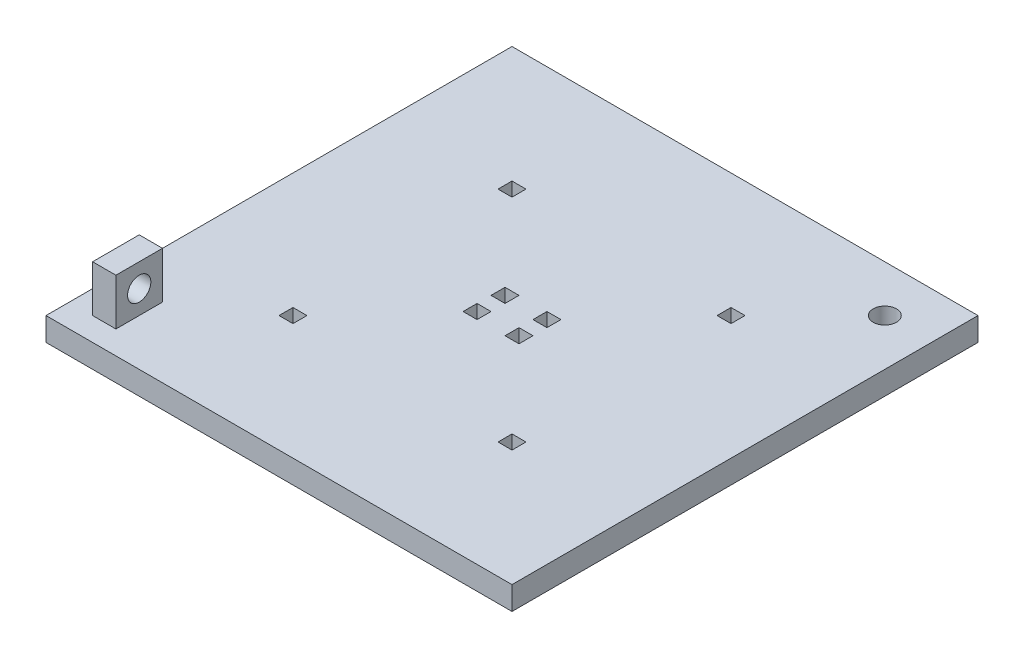
SolidWorks part; units mm, degrees
ref_plane "Front Plane" through (0, 0, 0) normal (0, 0, 1) x (1, 0, 0)
ref_plane "Top Plane" through (0, 0, 0) normal (0, 1, 0) x (1, 0, 0)
ref_plane "Right Plane" through (0, 0, 0) normal (1, 0, 0) x (0, 0, -1)
sketch "Sketch1" plane through (0, 0, 0) normal (0, 1, 0) x (1, 0, 0)
  line L0 (0, 50) -> (0, -50) construction
  line L1 (-50, 50) -> (50, 50)
  line L2 (-50, 50) -> (-50, -50)
  line L3 (-50, -50) -> (50, -50)
  line L4 (50, 50) -> (50, -50)
  line L5 (-25, 25) -> (-22, 25)
  line L6 (-25, 25) -> (-25, 22)
  line L7 (-25, 22) -> (-22, 22)
  line L8 (-22, 25) -> (-22, 22)
  line L9 (-50, 0) -> (50, 0) construction
  line L10 (22, 25) -> (22, 22)
  line L11 (25, 22) -> (22, 22)
  line L12 (25, 25) -> (25, 22)
  line L13 (25, 25) -> (22, 25)
  line L14 (25, -25) -> (22, -25)
  line L15 (25, -25) -> (25, -22)
  line L16 (25, -22) -> (22, -22)
  line L17 (22, -25) -> (22, -22)
  line L18 (-22, -25) -> (-22, -22)
  line L19 (-25, -22) -> (-22, -22)
  line L20 (-25, -25) -> (-25, -22)
  line L21 (-25, -25) -> (-22, -25)
  line L22 (3, 4.5) -> (3, 1.5)
  line L23 (-6, 4.5) -> (-3, 4.5)
  line L24 (-6, 4.5) -> (-6, 1.5)
  line L25 (-6, 1.5) -> (-3, 1.5)
  line L26 (-3, 4.5) -> (-3, 1.5)
  line L27 (6, 1.5) -> (3, 1.5)
  line L28 (6, 4.5) -> (6, 1.5)
  line L29 (6, 4.5) -> (3, 4.5)
  line L30 (6, -4.5) -> (3, -4.5)
  line L31 (6, -4.5) -> (6, -1.5)
  line L32 (6, -1.5) -> (3, -1.5)
  line L33 (-3, -4.5) -> (-3, -1.5)
  line L34 (-6, -1.5) -> (-3, -1.5)
  line L35 (-6, -4.5) -> (-6, -1.5)
  line L36 (-6, -4.5) -> (-3, -4.5)
  line L37 (3, -4.5) -> (3, -1.5)
  circle A0 centre (40, 40) radius 2.5
  point P12 (-50, 0)
  point P17 (0, 0)
  point P19 (-23.5, 25)
  dimension "D10" = 5
  dimension "D11" = 10
  dimension "D12" = 10
  dimension "D1" = 100
  dimension "D2" = 100
  dimension "D3" = 3
  dimension "D4" = 25
  dimension "D5" = 25
  dimension "D6" = 3
  dimension "D7" = 3
  dimension "D8" = 6
  dimension "D9" = 3
extrude "Boss-Extrude1" add sketch "Sketch1" along normal blind 5
sketch "Sketch4" plane through (0, 5, 0) normal (0, 1, 0) x (1, 0, 0)
  line L0 (-50, 50) -> (-50, -50) construction
  line L1 (-45, -35) -> (-40, -35)
  line L2 (-45, -35) -> (-45, -45)
  line L3 (-45, -45) -> (-40, -45)
  line L4 (-40, -35) -> (-40, -45)
  line L5 (-50, -50) -> (50, -50) construction
  dimension "D1" = 10
  dimension "D2" = 5
  dimension "D3" = 5
  dimension "D4" = 5
extrude "Boss-Extrude2" add sketch "Sketch4" along normal blind 10
sketch "Sketch5" plane through (-45, 0, 0) normal (-1, 0, 0) x (0, 0, 1)
  line L0 (35, 15) -> (45, 15) construction
  line L2 (-50, 0) -> (50, 0) construction
  circle A0 centre (40, 10) radius 2.5
  point P4 (40, 15)
  point P5 (40, 15.9745)
  dimension "D1" = 5
  dimension "D2" = 10
extrude "Cut-Extrude1" cut sketch "Sketch5" against normal blind 15
